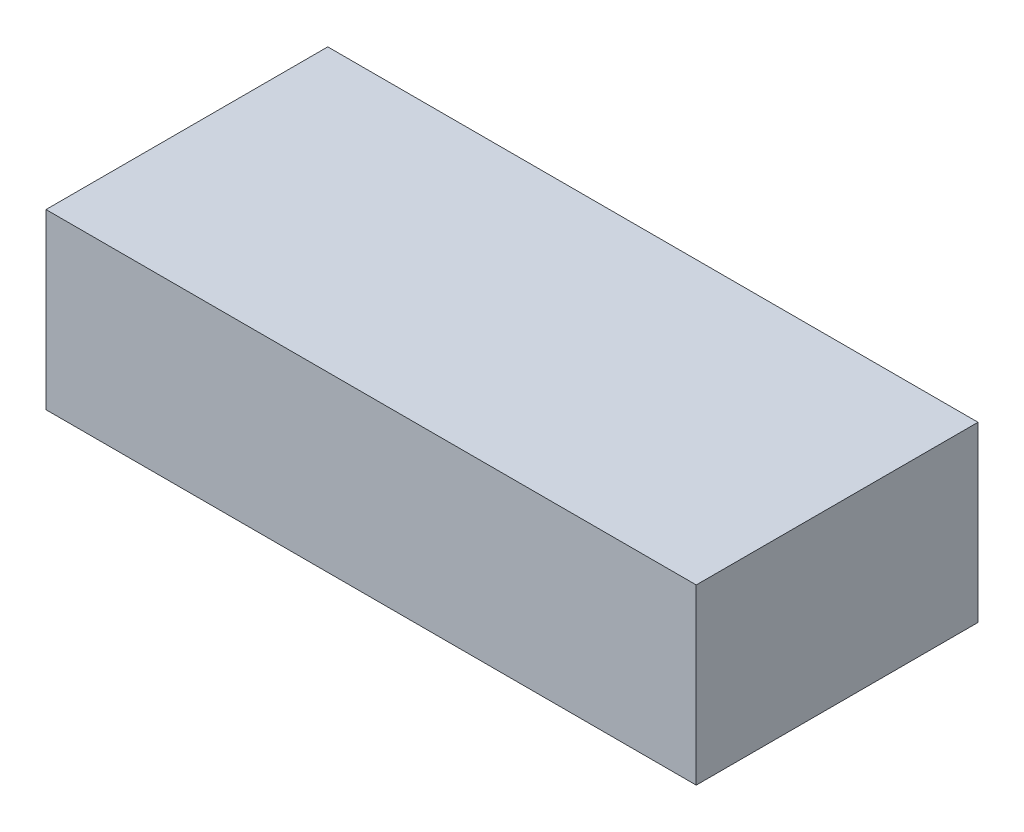
SolidWorks part; units mm, degrees
ref_plane "Front Plane" through (0, 0, 0) normal (0, 0, 1) x (1, 0, 0)
ref_plane "Top Plane" through (0, 0, 0) normal (0, 1, 0) x (1, 0, 0)
ref_plane "Right Plane" through (0, 0, 0) normal (1, 0, 0) x (0, 0, -1)
sketch "Sketch1" plane through (0, 0, 0) normal (0, 1, 0) x (1, 0, 0)
  line L1 (-75, -32.5) -> (75, -32.5)
  line L2 (-75, -32.5) -> (-75, 32.5)
  line L3 (-75, 32.5) -> (75, 32.5)
  line L4 (75, -32.5) -> (75, 32.5)
  line L5 (-75, -32.5) -> (75, 32.5) construction
  line L6 (-75, 32.5) -> (75, -32.5) construction
  point P0 (0, 0)
  dimension "D1" = 150
  dimension "D2" = 65
extrude "Boss-Extrude1" add sketch "Sketch1" along normal blind 40
sketch "Sketch2" plane through (0, 0, 0) normal (0, -1, 0) x (1, 0, 0)
  line L0 (-75, 32.5) -> (75, 32.5) construction
  line L1 (-71.952, -29.452) -> (71.952, -29.452)
  line L2 (-71.952, -29.452) -> (-71.952, 29.452)
  line L3 (-71.952, 29.452) -> (71.952, 29.452)
  line L4 (71.952, -29.452) -> (71.952, 29.452)
  line L5 (-71.952, -29.452) -> (71.952, 29.452) construction
  line L6 (-71.952, 29.452) -> (71.952, -29.452) construction
  line L7 (-75, -32.5) -> (-75, 32.5) construction
  point P0 (0, 0)
  dimension "D1" = 3.048
  dimension "D2" = 3.048
extrude "Cut-Extrude1" cut sketch "Sketch2" against normal blind 28.4
sketch "Sketch3" plane through (0, 0, -32.5) normal (0, 0, -1) x (-1, 0, 0)
  line L1 (75, 40) -> (75, 0) construction
  line L2 (-75, 0) -> (75, 0) construction
  circle A0 centre (38.12, 12.19) radius 4
  dimension "D3" = 8
  dimension "D1" = 36.88
  dimension "D2" = 12.19
extrude "Cut-Extrude2" cut sketch "Sketch3" against normal up to surface (3.048 mm away) up to face at (0, 14.2, -29.452)
